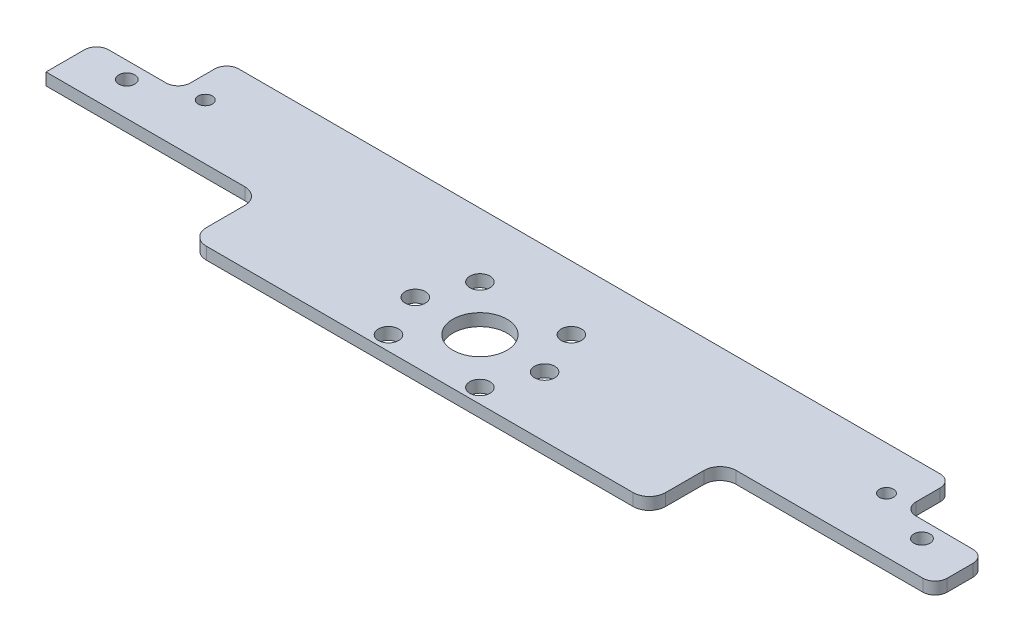
SolidWorks part; units mm, degrees
ref_plane "前视基准面" through (0, 0, 0) normal (0, 0, 1) x (1, 0, 0)
ref_plane "上视基准面" through (0, 0, 0) normal (0, 1, 0) x (1, 0, 0)
ref_plane "右视基准面" through (0, 0, 0) normal (1, 0, 0) x (0, 0, -1)
other "Configuration Table"
sketch "草图2" plane through (0, 0, 0) normal (0, 1, 0) x (1, 0, 0)
  line L0 (110, -9.1295) -> (-110, -9.1295)
  line L1 (110, -26.6295) -> (-110, -26.6295)
  line L2 (110, -26.6295) -> (110, 15.3705)
  line L3 (110, 15.3705) -> (-110, 15.3705)
  line L4 (-110, -26.6295) -> (-110, 15.3705)
  line L5 (-89.78, -4.7483) -> (-89.78, 18.2517) construction
  line L6 (-110, 3.3705) -> (-89.78, 3.3705)
  line L7 (56.8055, -9.1295) -> (56.8055, -26.6295)
  line L8 (0, -9.1295) -> (0, 15.3705)
  line L9 (-56.8055, -9.1295) -> (-56.8055, -26.6295)
  line L10 (-89.78, 3.3705) -> (-89.78, 15.3705)
  line L11 (89.78, 3.3705) -> (89.78, 15.3705)
  line L12 (110, 3.2517) -> (89.78, 3.3705)
  circle A0 centre (0, -11.7483) radius 6.682
  circle A1 centre (11.3137, -0.4346) radius 2.5
  circle A2 centre (0, -11.7483) radius 16
  circle A3 centre (16, -11.7483) radius 2.5
  circle A4 centre (11.3137, -23.062) radius 2.5
  circle A5 centre (0, -27.7483) radius 2.5
  circle A6 centre (-11.3137, -23.062) radius 2.5
  circle A7 centre (-16, -11.7483) radius 2.5
  circle A8 centre (-11.3137, -0.4346) radius 2.5
  circle A9 centre (0, 4.2517) radius 2.5
  circle A10 centre (-84.28, 4.5611) radius 1.75
  circle A11 centre (-98.3832, -0.7483) radius 2
  circle A12 centre (98.3832, -0.7483) radius 2
  circle A13 centre (84.28, 4.5611) radius 1.75
  point P0 (0, 0)
  point P20 (-98.3832, -0.7483)
  point P37 (0, -11.7483)
  dimension "D3" = 5
  dimension "D6" = 3.5
  dimension "D7" = 4
  dimension "D1" = 220
  dimension "D2" = 17.5
  dimension "D5" = 42
  dimension "D8" = 12
  dimension "D4" = 8
extrude "凸台-拉伸1" add sketch "草图2" along normal blind 3 contours A7 A2 A6 L1 A5 A4 A3 L0 A0 | A9 L8 A0 L0 A2 A1 | A9 A2 A8 L0 A0 L8 | A9 L8 L3 L4 L0 A2 A8 | A9 A2 A1 L0 L2 L3 L8 | L1 A5 | A4 A2 L1 L7 L0 A3 | A7 L0 L9 L1 A2 A6
fillet "圆角1" radius 4 4 edges at (56.8055, 1.5, 9.1295) (56.8055, 1.5, 26.6295) (-56.8055, 1.5, 9.1295) (-56.8055, 1.5, 26.6295)
fillet "圆角2" radius 3 7 edges at (-110, 1.5, -3.3705) (-89.78, 1.5, -3.3705) (-89.78, 1.5, -15.3705) (110, 1.5, 9.1295) (110, 1.5, -3.2517) (89.78, 1.5, -3.3705) (89.78, 1.5, -15.3705)
